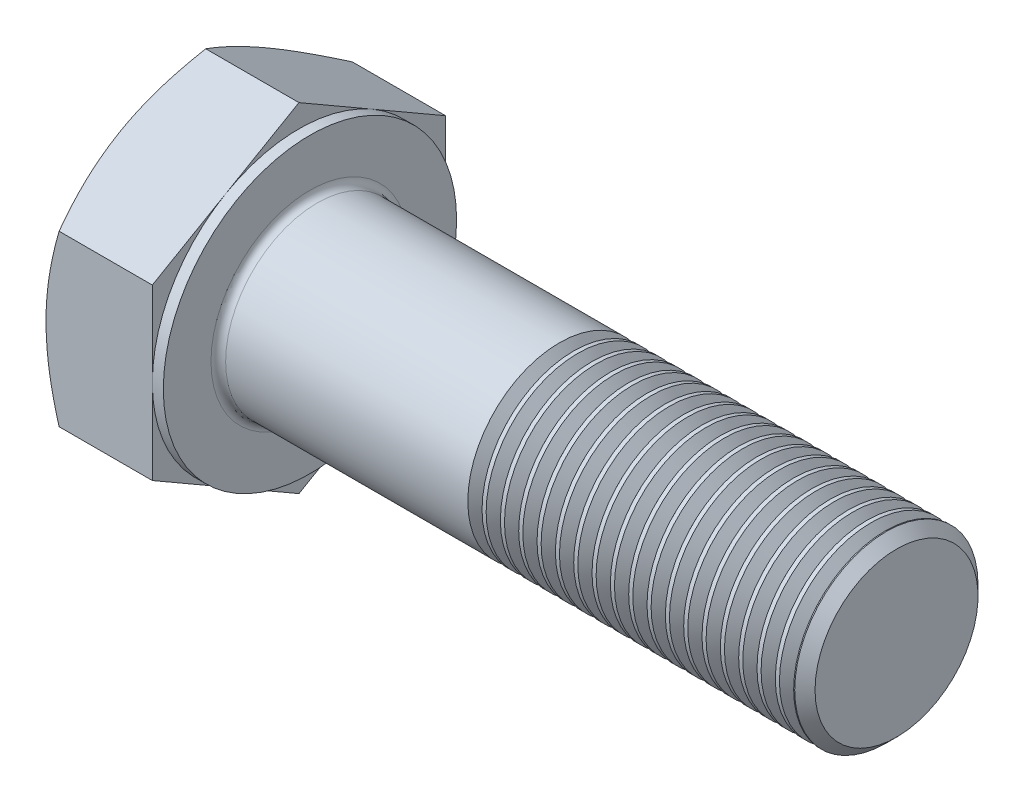
SolidWorks part; units mm, degrees
ref_plane "Plane1" through (0, 0, 0) normal (0, 0, 1) x (1, 0, 0)
ref_plane "Plane2" through (0, 0, 0) normal (0, 1, 0) x (1, 0, 0)
ref_plane "Plane3" through (0, 0, 0) normal (1, 0, 0) x (0, 0, -1)
sketch "Sketch1" plane through (0, 0, 0) normal (1, 0, 0) x (0, 0, -1)
  line L0 (8, 4.6188) -> (8, -4.6188)
  line L1 (-8, 4.6188) -> (-8, -4.6188)
  line L2 (8, -4.6188) -> (0, -9.2376)
  line L3 (0, -9.2376) -> (-8, -4.6188)
  line L4 (8, 4.6188) -> (0, 9.2376)
  line L5 (0, 9.2376) -> (-8, 4.6188)
  dimension "Width_flats" = 16
  dimension "D2" = 120
  dimension "D3" = 8
  dimension "D4" = 8
  dimension "D5" = 8
extrude "BaseHead" add sketch "Sketch1" along normal blind 6.4
sketch "BodySke" plane through (0, 0, 0) normal (0, 0, 1) x (1, 0, 0)
  line L0 (0, 4.6188) -> (0, -4.6188) construction
  line L1 (0, 0) -> (38.4, 0)
  line L2 (0, 0) -> (0, 5)
  line L3 (0, 5) -> (37.8455, 5)
  line L4 (38.4, 0) -> (38.4, 4.4455)
  line L5 (6.4, 9.2376) -> (6.4, 4.6188) construction
  line L6 (38.4, 4.4455) -> (37.8455, 5)
  line L7 (0, 0) -> (96.52, 0) construction
  line L8 (38.4, -4.4455) -> (37.8455, -5) construction
  line L9 (0, -5) -> (37.8455, -5) construction
  line L10 (7.4, 15.24) -> (7.4, -1.27) construction
  line L11 (20.4, 15.24) -> (20.4, -1.27) construction
  line L12 (6.4, 4.6188) -> (6.4, -4.6188) construction
  dimension "Length" = 32
  dimension "Body_ch_ang" = 45
  dimension "Diameter" = 10
  dimension "Minor_dia" = 8.891
  dimension "Advance" = 1
  dimension "Thread_nom" = 18
revolve "BaseBody" add sketch "BodySke"
cosmetic thread "ThreadCosmetic" [suppressed]
fillet "HeadFillet" radius 0.4 1 edges at (6.4, 0, -5)
sketch "Sketch3" plane through (0, 0, 0) normal (0, 0, 1) x (1, 0, 0)
  line L0 (0, 8) -> (3.6013, 14.2376)
  line L1 (0, 9.2376) -> (0, 4.6188) construction
  line L2 (3.6013, 14.2376) -> (3.6013, 19.2376)
  line L3 (3.6013, 19.2376) -> (-10, 19.2376)
  line L4 (-10, 19.2376) -> (-10, 8)
  line L5 (-10, 8) -> (0, 8)
  line L6 (0, 0) -> (99.06, 0) construction
  line L7 (6.4, 9.2376) -> (0, 9.2376) construction
  dimension "D1" = 8
  dimension "D2" = 5
  dimension "D3" = 10
  dimension "D4" = 5
  dimension "Head_ch_ang" = 30
revolve "HeadChamfer" cut sketch "Sketch3" angle 360 about L6
sketch "Sketch4" plane through (0, 0, 0) normal (0, 0, 1) x (1, 0, 0)
  line L1 (6.4, 9.2376) -> (6.4, 4.6188) construction
  line L2 (6.4, 8) -> (5.8, 8)
  line L3 (6.4, 8) -> (6.4, 19.2376)
  line L4 (6.4, 19.2376) -> (5.8, 19.2376)
  line L5 (0, 0) -> (95.25, 0) construction
  line L6 (0, 0) -> (96.52, 0) construction
  line L7 (5.8, 8) -> (5.8, 19.2376)
  line L8 (6.4, 9.2376) -> (0.7145, 9.2376) construction
  dimension "D1" = 16
  dimension "D2" = 10
  dimension "Bearing_ht" = 0.6
revolve "BearingFace" cut sketch "Sketch4" angle 360 about L5
sketch "ThdSchSke" plane through (0, 0, 0) normal (0, 0, 1) x (1, 0, 0)
  line L0 (20.4, -4.4455) -> (20.0117, -5)
  line L1 (20.4, -4.4455) -> (20.7883, -5)
  line L2 (20.7883, -5) -> (20.7883, -6.25)
  line L3 (-3.175, 0) -> (5.1513, 0) construction
  line L5 (20.7883, -6.25) -> (20.0117, -6.25)
  line L6 (20.0117, -6.25) -> (20.0117, -5)
  dimension "Thread_minor" = 8.891
  dimension "Diameter" = 10
  dimension "Start" = 20.4
  dimension "SideAngle" = 55
  dimension "VeeAngle" = 70
  dimension "Overcut" = 12.5
revolve "ThreadSchematic" cut sketch "ThdSchSke" angle 360 about L3
pattern_linear "ThdSchPat" count 18 spacing 1 along (1, 0, 0) of "ThreadSchematic"
equation "\"D3@Sketch1\" = \"Width_flats@Sketch1\" / 2"
equation "\"D4@Sketch1\" = \"D3@Sketch1\""
equation "\"D5@Sketch1\" = \"D4@Sketch1\""
equation "\"Thread_minor@ThreadCosmetic\" = \"Minor_dia@BodySke\""
equation "\"D1@Sketch3\" = \"Width_flats@Sketch1\" / 2"
equation "\"D1@Sketch4\" = \"Width_flats@Sketch1\""
equation "\"Thread_length@ThreadCosmetic\" = ((sgn( (\"Length@BodySke\" - \"Advance@BodySke\" ) - \"Thread_nom@BodySke\" )-1)*( (\"Length@BodySke\" - \"Advance@BodySke\" ) - \"Thread_nom@BodySke\" ))/-2+ \"Thread_nom@BodySke\""
equation "\"Thread_minor@ThdSchSke\" = \"Minor_dia@BodySke\""
equation "\"Diameter@ThdSchSke\" = \"Diameter@BodySke\""
equation "\"Overcut@ThdSchSke\" = \"Diameter@BodySke\" * 1.25"
equation "\"Start@ThdSchSke\" = \"Head_ht@BaseHead\" + \"Length@BodySke\" - \"Thread_length@ThreadCosmetic\"  '---Non-countersunk---"
equation "\"Num_threads@ThdSchPat\" = int( \"Thread_length@ThreadCosmetic\" / \"Advance@BodySke\" + 0.999 )  + 1"
equation "\"Advance@ThdSchPat\" = \"Thread_length@ThreadCosmetic\" /  (\"Num_threads@ThdSchPat\" - 1) 'relax it"
equation "\"Num_threads@ThdSchPat\" = \"Num_threads@ThdSchPat\" - sgn( \"Num_threads@ThdSchPat\" - 1) '---chamfered tips only---"
